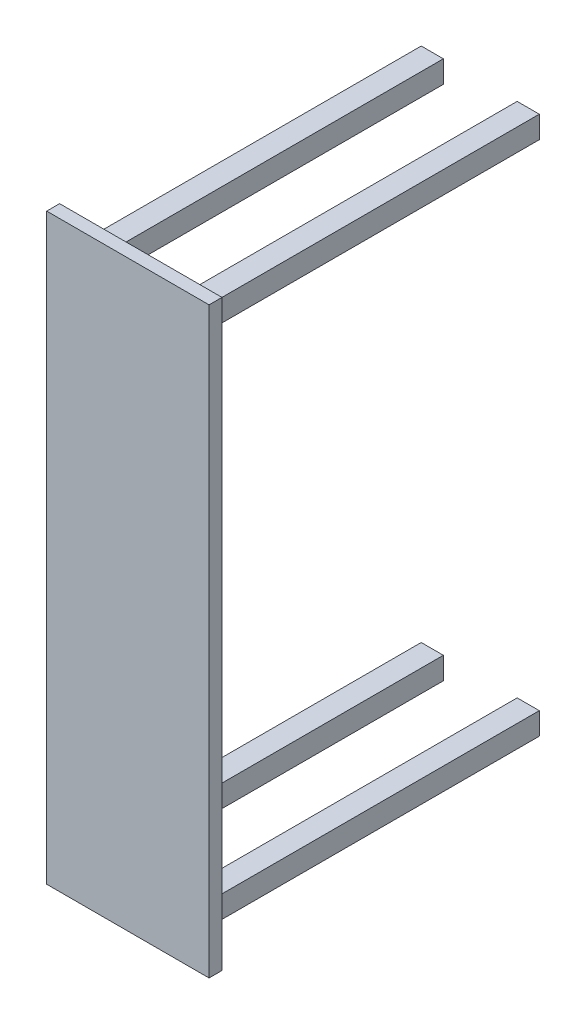
SolidWorks part; units mm, degrees
ref_plane "Front Plane" through (0, 0, 0) normal (0, 0, 1) x (1, 0, 0)
ref_plane "Top Plane" through (0, 0, 0) normal (0, 1, 0) x (1, 0, 0)
ref_plane "Right Plane" through (0, 0, 0) normal (1, 0, 0) x (0, 0, -1)
sketch "Sketch1" plane through (0, 0, 0) normal (0, 0, 1) x (1, 0, 0)
  line L1 (-279.4, 1003.3) -> (279.4, 1003.3)
  line L2 (-279.4, 1003.3) -> (-279.4, -1003.3)
  line L3 (-279.4, -1003.3) -> (279.4, -1003.3)
  line L4 (279.4, 1003.3) -> (279.4, -1003.3)
  line L5 (-279.4, 1003.3) -> (279.4, -1003.3) construction
  line L6 (-279.4, -1003.3) -> (279.4, 1003.3) construction
  point P0 (0, 0)
  dimension "D1" = 558.8
  dimension "D2" = 2006.6
extrude "Boss-Extrude1" add sketch "Sketch1" along normal blind 44.45
sketch "Sketch5" plane through (0, 0, 0) normal (0, 0, -1) x (-1, 0, 0)
  line L1 (-203.2, 927.1) -> (-127, 927.1)
  line L2 (-203.2, 927.1) -> (-203.2, 850.9)
  line L3 (-203.2, 850.9) -> (-127, 850.9)
  line L4 (-127, 927.1) -> (-127, 850.9)
  line L5 (127, 927.1) -> (203.2, 927.1)
  line L6 (127, 927.1) -> (127, 850.9)
  line L7 (127, 850.9) -> (203.2, 850.9)
  line L8 (203.2, 927.1) -> (203.2, 850.9)
  line L9 (-203.2, -850.9) -> (-127, -850.9)
  line L10 (-203.2, -850.9) -> (-203.2, -927.1)
  line L11 (-203.2, -927.1) -> (-127, -927.1)
  line L12 (-127, -850.9) -> (-127, -927.1)
  line L13 (127, -850.9) -> (203.2, -850.9)
  line L14 (127, -850.9) -> (127, -927.1)
  line L15 (127, -927.1) -> (203.2, -927.1)
  line L16 (203.2, -850.9) -> (203.2, -927.1)
  line L17 (-279.4, -1003.3) -> (-279.4, 1003.3) construction
  line L18 (279.4, 1003.3) -> (279.4, -1003.3) construction
  line L19 (-279.4, 1003.3) -> (279.4, 1003.3) construction
  line L20 (279.4, -1003.3) -> (-279.4, -1003.3) construction
  dimension "D1" = 76.2
  dimension "D2" = 76.2
  dimension "D3" = 76.2
  dimension "D4" = 76.2
  dimension "D5" = 76.2
  dimension "D6" = 76.2
  dimension "D7" = 76.2
  dimension "D8" = 76.2
  dimension "D9" = 76.2
extrude "Boss-Extrude2" add sketch "Sketch5" along normal blind 1168.4
